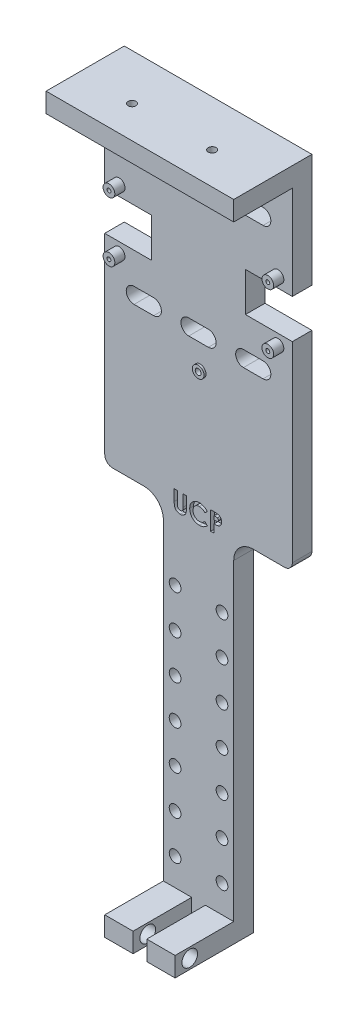
SolidWorks part; units mm, degrees
ref_plane "Plano frontal" through (0, 0, 0) normal (0, 0, 1) x (1, 0, 0)
ref_plane "Plano superior" through (0, 0, 0) normal (0, 1, 0) x (1, 0, 0)
ref_plane "Plano direito" through (0, 0, 0) normal (1, 0, 0) x (0, 0, -1)
other "Caixa delimitadora"
ref_plane "Default Plane" through (-24, 90, -2.5) normal (1, 0, 0) x (0, 0, -1)
sketch "Esboço1" plane through (0, 0, 0) normal (0, 0, 1) x (1, 0, 0)
  line L1 (-9, -90) -> (9, -90)
  line L2 (-9, -90) -> (-9, 90)
  line L3 (-9, 90) -> (9, 90)
  line L4 (9, -90) -> (9, 90)
  line L5 (-9, -90) -> (9, 90) construction
  line L6 (-9, 90) -> (9, -90) construction
  point P0 (0, 0)
  dimension "D1" = 18
  dimension "D2" = 180
extrude "Ressalto-extrusão1" add sketch "Esboço1" along normal mid plane 5
sketch "Esboço2" plane through (0, 0, 2.5) normal (0, 0, 1) x (1, 0, 0)
  line L0 (0, -11) -> (0, 11) construction
  line L1 (-9, -90) -> (-1.75, -90)
  line L2 (-9, -90) -> (-9, -85)
  line L3 (-9, -85) -> (-1.75, -85)
  line L4 (-1.75, -90) -> (-1.75, -85)
  line L5 (9, -85) -> (1.75, -85)
  line L6 (1.75, -90) -> (1.75, -85)
  line L7 (9, -90) -> (1.75, -90)
  line L8 (9, -90) -> (9, -85)
  dimension "D1" = 7.25
  dimension "D2" = 5
extrude "Ressalto-extrusão2" add sketch "Esboço2" along normal blind 15
sketch "Esboço5" plane through (0, 0, 2.5) normal (0, 0, 1) x (1, 0, 0)
  line L0 (-1.75, -90) -> (1.75, -90) construction
  line L1 (-9, 90) -> (-24, 90)
  line L2 (-9, 90) -> (-9, 0)
  line L3 (-9, 0) -> (-24, 0)
  line L4 (-24, 90) -> (-24, 0)
  line L5 (0, -11) -> (0, 11) construction
  line L6 (9, 0) -> (24, 0)
  line L7 (24, 90) -> (24, 0)
  line L8 (9, 90) -> (24, 90)
  line L9 (9, 90) -> (9, 0)
  dimension "D1" = 15
  dimension "D2" = 90
extrude "Ressalto-extrusão5" add sketch "Esboço5" against normal blind 5
sketch "Esboço3" plane through (0, 0, 2.5) normal (0, 0, 1) x (1, 0, 0)
  line L1 (-24, 90) -> (24, 90)
  line L2 (-24, 90) -> (-24, 85)
  line L3 (-24, 85) -> (24, 85)
  line L4 (24, 90) -> (24, 85)
  line L5 (-24, 90) -> (-24, 0) construction
  line L7 (24, 0) -> (24, 90) construction
  line L8 (24, 90) -> (-24, 90) construction
  dimension "D1" = 5
extrude "Ressalto-extrusão3" add sketch "Esboço3" along normal blind 15
fillet "Filete1" radius 2 2 edges at (24, 0, 0) (-24, 0, 0)
sketch "Esboço6" plane through (0, 0, 2.5) normal (0, 0, 1) x (1, 0, 0)
  circle A1 centre (-20.32, 63.62) radius 0.5
  circle A8 centre (20.32, 63.62) radius 0.5
  circle A9 centre (20.32, 48.38) radius 0.5
  circle A10 centre (-20.32, 48.38) radius 0.5
  circle A12 centre (0.4, 32.75) radius 0.75
  dimension "D1" = 1
  dimension "D2" = 1.5
extrude "Corte-extrusão1" cut sketch "Esboço6" against normal through all both and the other way through all
sketch "Esboço7" plane through (0, 90, 0) normal (0, 1, 0) x (1, 0, 0)
  circle A0 centre (-10.25, -9.27) radius 1
  circle A1 centre (10.25, -9.27) radius 1
  dimension "D1" = 2
  dimension "D2" = 2
sketch "Esboço8" plane through (0, 0, 2.5) normal (0, 0, 1) x (1, 0, 0)
  line L0 (-24, 85) -> (-24, 2) construction
  line L1 (-24, 61) -> (-12, 61)
  line L2 (-24, 61) -> (-24, 51)
  line L3 (-24, 51) -> (-12, 51)
  line L4 (-12, 61) -> (-12, 51)
  line L5 (-21.6, 65) -> (21.6, 65) construction
  line L7 (0, -11) -> (0, 11) construction
  line L8 (24, 51) -> (12, 51)
  line L9 (12, 61) -> (12, 51)
  line L10 (24, 61) -> (12, 61)
  line L11 (24, 61) -> (24, 51)
  dimension "D1" = 12
  dimension "D2" = 10
  dimension "D3" = 4
extrude "Corte-extrusão2" cut sketch "Esboço7" against normal up to next and the other way through all
extrude "Corte-extrusão3" cut sketch "Esboço8" against normal up to next
fillet "Filete2" radius 5 2 edges at (-9, 0, 0) (9, 0, 0)
sketch "Esboço10" plane through (0, 0, 2.5) normal (0, 0, 1) x (1, 0, 0)
  line L0 (-16.5, 75) -> (-11.5, 75) construction
  line L5 (-16.5, 77) -> (-11.5, 77)
  line L6 (-16.5, 73) -> (-11.5, 73)
  line L7 (-24, 85) -> (-24, 61) construction
  line L8 (-2.5, 73) -> (2.5, 73)
  line L9 (-2.5, 77) -> (2.5, 77)
  line L10 (-2.5, 75) -> (2.5, 75) construction
  line L11 (11.5, 73) -> (16.5, 73)
  line L12 (11.5, 77) -> (16.5, 77)
  line L13 (11.5, 75) -> (16.5, 75) construction
  line L14 (24, 61) -> (24, 85) construction
  line L15 (24, 90) -> (-24, 90) construction
  line L17 (-16.5, 39) -> (-11.5, 39)
  line L18 (-16.5, 43) -> (-11.5, 43)
  line L19 (-16.5, 41) -> (-11.5, 41) construction
  line L20 (-2.5, 43) -> (2.5, 43)
  line L21 (-2.5, 39) -> (2.5, 39)
  line L22 (-2.5, 41) -> (2.5, 41) construction
  line L23 (11.5, 43) -> (16.5, 43)
  line L24 (11.5, 39) -> (16.5, 39)
  line L25 (11.5, 41) -> (16.5, 41) construction
  line L26 (24, 2) -> (24, 51) construction
  arc A0 (-16.5, 77) -> (-16.5, 73) centre (-16.5, 75) ccw
  arc A1 (-11.5, 73) -> (-11.5, 77) centre (-11.5, 75) ccw
  arc A2 (-2.5, 77) -> (-2.5, 73) centre (-2.5, 75) ccw
  arc A3 (2.5, 73) -> (2.5, 77) centre (2.5, 75) ccw
  arc A4 (11.5, 77) -> (11.5, 73) centre (11.5, 75) ccw
  arc A5 (16.5, 73) -> (16.5, 77) centre (16.5, 75) ccw
  arc A6 (-16.5, 43) -> (-16.5, 39) centre (-16.5, 41) ccw
  arc A7 (-11.5, 39) -> (-11.5, 43) centre (-11.5, 41) ccw
  arc A8 (2.5, 39) -> (2.5, 43) centre (2.5, 41) ccw
  arc A9 (-2.5, 43) -> (-2.5, 39) centre (-2.5, 41) ccw
  arc A10 (16.5, 39) -> (16.5, 43) centre (16.5, 41) ccw
  arc A11 (11.5, 43) -> (11.5, 39) centre (11.5, 41) ccw
  point P2 (-14, 75)
  point P12 (0, 75)
  point P19 (14, 75)
  point P30 (-14, 41)
  point P37 (0, 41)
  point P44 (14, 41)
  dimension "D6" = 2
  dimension "D1" = 7.5
  dimension "D3" = 5
  dimension "D4" = 7.5
  dimension "D5" = 15
  dimension "D8" = 34
  dimension "D10" = 7.5
  dimension "D2" = 3
  dimension "D7" = 2
  dimension "D9" = 3
extrude "Corte-extrusão4" cut sketch "Esboço10" against normal through all both and the other way through all
sketch "Esboço11" plane through (0, 0, 2.5) normal (0, 0, 1) x (1, 0, 0)
  line L0 (-10.4645, -1.4645) -> (10.4645, -1.4645) construction
  arc A0 (-9, -5) -> (-14, 0) centre (-14, -5) ccw construction
  arc A1 (14, 0) -> (9, -5) centre (14, -5) ccw construction
  text T0 "<b>UCP</b>" font "Century Gothic" height in points 18
extrude "Corte-extrusão6" cut sketch "Esboço11" against normal blind 1 and the other way through all
sketch "Esboço12" plane through (9, 0, 0) normal (1, 0, 0) x (0, 0, -1)
  circle A0 centre (-13.75, -87.5) radius 2
  dimension "D1" = 4
extrude "Corte-extrusão7" cut sketch "Esboço12" against normal through all both and the other way through all
sketch "Esboço13" plane through (0, 0, 2.5) normal (0, 0, 1) x (1, 0, 0)
  line L0 (9, -85) -> (9, -5) construction
  line L1 (-9, -5) -> (-9, -85) construction
  line L2 (-9, -90) -> (-1.75, -90) construction
  circle A0 centre (-6, -78) radius 1.5
  circle A1 centre (6, -78) radius 1.5
  circle A2 centre (6, -68) radius 1.5
  circle A3 centre (6, -58) radius 1.5
  circle A4 centre (6, -48) radius 1.5
  circle A5 centre (6, -38) radius 1.5
  circle A6 centre (6, -28) radius 1.5
  circle A7 centre (6, -18) radius 1.5
  circle A8 centre (-6, -68) radius 1.5
  circle A9 centre (-6, -58) radius 1.5
  circle A10 centre (-6, -48) radius 1.5
  circle A11 centre (-6, -38) radius 1.5
  circle A12 centre (-6, -28) radius 1.5
  circle A13 centre (-6, -18) radius 1.5
  dimension "D1" = 3
  dimension "D4" = 3
  dimension "D5" = 3
  dimension "D6" = 10
  dimension "D7" = 12
  dimension "D8" = 3
  dimension "D2" = 2
  dimension "D3" = 7
extrude "Corte-extrusão8" cut sketch "Esboço13" against normal through all both and the other way through all
sketch "Esboço14" plane through (0, 0, 2.5) normal (0, 0, 1) x (1, 0, 0)
  circle A0 centre (20.32, 48.38) radius 1.5
  circle A1 centre (20.32, 48.38) radius 0.5
  circle A2 centre (-20.32, 48.38) radius 0.5
  circle A3 centre (-20.32, 63.62) radius 0.5
  circle A4 centre (20.32, 63.62) radius 0.5
  circle A5 centre (20.32, 63.62) radius 1.5
  circle A6 centre (-20.32, 48.38) radius 1.5
  circle A7 centre (-20.32, 63.62) radius 1.5
  circle A8 centre (20.32, 48.38) radius 0.5 construction
  circle A9 centre (-20.32, 48.38) radius 0.5 construction
  circle A10 centre (-20.32, 63.62) radius 0.5 construction
  circle A11 centre (20.32, 63.62) radius 0.5 construction
  dimension "D1" = 3
extrude "Ressalto-extrusão6" add sketch "Esboço14" along normal blind 2.6
sketch "Esboço15" plane through (0, 0, 2.5) normal (0, 0, 1) x (1, 0, 0)
  circle A0 centre (0.4, 32.75) radius 1.5
  circle A1 centre (0.4, 32.75) radius 0.75
  circle A2 centre (0.4, 32.75) radius 0.75 construction
  dimension "D1" = 3
extrude "Ressalto-extrusão7" add sketch "Esboço15" along normal blind 0.5
